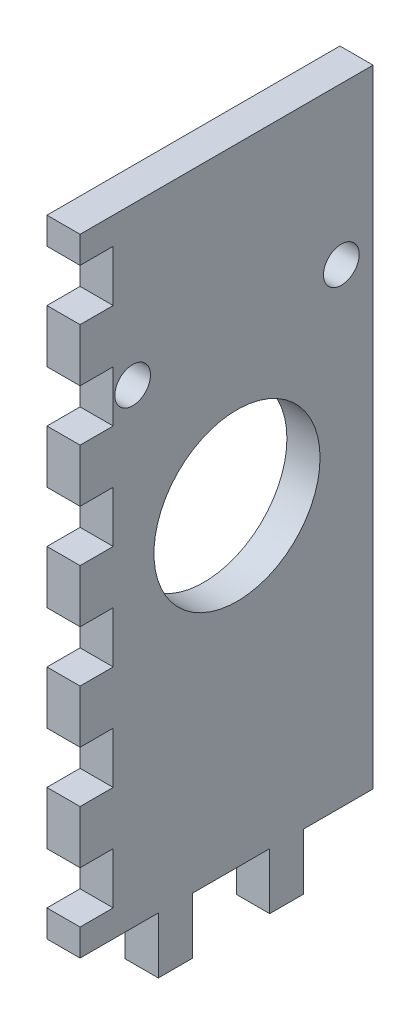
SolidWorks part; units mm, degrees
ref_plane "Front Plane" through (0, 0, 0) normal (0, 0, 1) x (1, 0, 0)
ref_plane "Top Plane" through (0, 0, 0) normal (0, 1, 0) x (1, 0, 0)
ref_plane "Right Plane" through (0, 0, 0) normal (1, 0, 0) x (0, 0, -1)
sketch "Sketch1" plane through (0, 0, 0) normal (0, 1, 0) x (1, 0, 0)
  line L0 (0, 0) -> (-50.5, 0) construction
  line L1 (0, 0) -> (0, 50.5) construction
  line L2 (-50.5, 22.5) -> (-22.5, 22.5)
  line L3 (-22.5, 22.5) -> (-22.5, 50.5)
  line L5 (-22.5, 22.5) -> (-50.5, 22.5)
  line L6 (-22.5, 22.5) -> (-22.5, 25.675)
  line L7 (-22.5, 25.675) -> (-50.5, 25.675)
  line L8 (-50.5, 22.5) -> (-50.5, 25.675)
  line L9 (-22.5, 22.5) -> (-25.675, 22.5)
  line L10 (-22.5, 22.5) -> (-22.5, 50.5)
  line L11 (-22.5, 50.5) -> (-25.675, 50.5)
  line L12 (-25.675, 22.5) -> (-25.675, 50.5)
  point P7 (-37.5, 22.5)
  point P8 (-22.5, 37.5)
  dimension "D1" = 50.5
  dimension "D2" = 50.5
  dimension "D3" = 22.5
  dimension "D4" = 22.5
  dimension "D5" = 37.5
  dimension "D6" = 37.5
  dimension "D7" = 28
  dimension "D8" = 28
  dimension "D9" = 3.175
  dimension "D10" = 3.175
extrude "Boss-Extrude1" add sketch "Sketch1" along normal blind 60 contours L2 L12 L7 L8 | L12 L5 L3 L7 | L12 L7 L3 L11
sketch "Sketch2" plane through (0, 0, -22.5) normal (0, 0, 1) x (1, 0, 0)
  line L0 (-50.5, 30) -> (-22.5, 30) construction
  line L1 (-50.5, 60) -> (-50.5, 0) construction
  line L2 (-22.5, 60) -> (-22.5, 0) construction
  line L3 (-37.5, 60) -> (-37.5, 0) construction
  line L4 (-50.5, 60) -> (-22.5, 60) construction
  line L5 (-50.5, 0) -> (-22.5, 0) construction
  line L7 (-50.5, 60) -> (-22.5758, 60)
  line L15 (-33.125, -5.4) -> (-33.125, 0)
  line L16 (-30, -5.4) -> (-33.125, -5.4)
  line L17 (-30, -5.4) -> (-30, 0)
  line L18 (-40.625, -5.4) -> (-40.625, 0)
  line L19 (-43.75, -5.4) -> (-40.625, -5.4)
  line L20 (-43.75, -5.4) -> (-43.75, 0)
  circle A0 centre (-37.5, 30) radius 8
  dimension "D2" = 16
  dimension "D1" = 15
  dimension "D3" = 5.4
  dimension "D4" = 7.5
  dimension "D6" = 3.125
  dimension "D5" = 7.5
sketch "Sketch3" plane through (-22.5, 0, 0) normal (1, 0, 0) x (0, 0, -1)
  line L0 (22.5, 30) -> (50.5, 30) construction
  line L1 (22.5, 60) -> (22.5, 0) construction
  line L2 (50.5, 60) -> (50.5, 0) construction
  line L3 (37.5, 60) -> (37.5, 0) construction
  line L4 (22.5, 60) -> (50.5, 60) construction
  line L5 (22.5, 0) -> (50.5, 0) construction
  circle A0 centre (37.5, 30) radius 8
  dimension "D1" = 16
  dimension "D2" = 15
extrude "Boss-Extrude4" add sketch "Sketch2" against normal blind 3.175
sketch "Sketch4" plane through (0, 0, -22.5) normal (0, 0, 1) x (1, 0, 0)
  line L0 (-50.5, 30) -> (-22.5, 30) construction
  line L1 (-50.5, 60) -> (-50.5, 0) construction
  line L2 (-22.5, 22) -> (-22.5, 38) construction
  line L3 (-37.5, 60) -> (-37.5, 0) construction
  line L4 (-50.5, 60) -> (-22.5, 60) construction
  line L5 (-50.5, 0) -> (-43.75, 0) construction
  line L6 (-22.5, 60) -> (-22.5, 0) construction
  circle A0 centre (-37.5, 30) radius 8
  dimension "D1" = 16
  dimension "D2" = 15
extrude "Cut-Extrude1" cut sketch "Sketch4" against normal blind 3.175
extrude "Cut-Extrude2" cut sketch "Sketch3" against normal blind 3.175
sketch "Sketch5" plane through (-22.5, 0, 0) normal (1, 0, 0) x (0, 0, -1)
  line L0 (22.5, 0) -> (50.5, 0) construction
  line L1 (22.5, 60) -> (50.5, 60)
  line L10 (22.5, 30) -> (50.5, 30) construction
  line L11 (22.5, 60) -> (22.5, 0) construction
  line L12 (50.5, 60) -> (50.5, 0) construction
  line L13 (43.85, -5.4) -> (43.85, 0)
  line L14 (40.675, -5.4) -> (43.85, -5.4)
  line L15 (40.675, -5.4) -> (40.675, 0)
  line L16 (33.175, -5.4) -> (33.175, 0)
  line L17 (30, -5.4) -> (33.175, -5.4)
  line L18 (30, -5.4) -> (30, 0)
  line L19 (30, 0) -> (33.175, 0)
  line L28 (40.675, 0) -> (43.85, 0)
  point P7 (37.5, 30)
  point P8 (-4.2304, -0.8722)
  point P10 (8.5502, 17.2274)
  dimension "D1" = 7.5
  dimension "D2" = 5.4
  dimension "D3" = 3.175
  dimension "D4" = 7.5
extrude "Boss-Extrude5" add sketch "Sketch5" against normal blind 3.175
sketch "Sketch6" plane through (0, 0, -22.5) normal (0, 0, 1) x (1, 0, 0)
  line L0 (-50.5, 45) -> (-22.5, 45) construction
  line L1 (-50.5, 60) -> (-50.5, 0) construction
  line L2 (-22.5, 60) -> (-22.5, 0) construction
  line L3 (-37.5, 60) -> (-37.5, 0) construction
  line L4 (-50.5, 60) -> (-22.5, 60) construction
  line L5 (-40.625, 0) -> (-33.125, 0) construction
  circle A0 centre (-37.5, 30) radius 8 construction
  circle A1 centre (-37.5, 30) radius 8 construction
  circle A2 centre (-47.5, 45) radius 1.75
  circle A3 centre (-27.5, 45) radius 1.75
  dimension "D1" = 15
  dimension "D3" = 3.5
  dimension "D2" = 10
extrude "Cut-Extrude3" cut sketch "Sketch6" against normal blind 10 contours A2 | A3
sketch "Sketch7" plane through (-22.5, 0, 0) normal (1, 0, 0) x (0, 0, -1)
  line L0 (37.5, 60) -> (37.5, 0) construction
  line L1 (22.5, 60) -> (50.5, 60) construction
  line L2 (33.175, 0) -> (40.675, 0) construction
  line L4 (22.5, 60) -> (22.5, 0) construction
  line L5 (22.5, 45) -> (50.5, 45) construction
  line L6 (50.5, 60) -> (50.5, 0) construction
  circle A0 centre (37.5, 30) radius 8 construction
  circle A1 centre (37.5, 30) radius 8 construction
  circle A2 centre (47.5, 45) radius 1.75
  circle A3 centre (27.5, 45) radius 1.75
  dimension "D1" = 15
  dimension "D3" = 3.5
  dimension "D2" = 10
extrude "Cut-Extrude4" cut sketch "Sketch7" against normal blind 10
sketch "Sketch9" plane through (-50.5, 0, 0) normal (-1, 0, 0) x (0, 0, 1)
  line L1 (-25.675, 60) -> (-22.5, 60)
  line L2 (-25.675, 60) -> (-25.675, -5.4)
  line L3 (-25.675, -5.4) -> (-22.5, -5.4)
  line L4 (-22.5, 60) -> (-22.5, -5.4)
extrude "Cut-Extrude5" cut sketch "Sketch9" along direction (-1, 0, 0) on the side against the normal up to surface (24.825 mm away)
sketch "Sketch10" plane through (-25.675, 0, 0) normal (-1, 0, 0) x (0, 0, 1)
  line L0 (-22.5, 60) -> (-22.5, 0) construction
  line L1 (-22.5, 57.5) -> (-25.675, 57.5)
  line L2 (-22.5, 57.5) -> (-22.5, 52.5)
  line L3 (-22.5, 52.5) -> (-25.675, 52.5)
  line L4 (-25.675, 57.5) -> (-25.675, 52.5)
  line L5 (-22.5, 47.5) -> (-25.675, 47.5)
  line L6 (-25.675, 47.5) -> (-25.675, 42.5)
  line L7 (-22.5, 42.5) -> (-25.675, 42.5)
  line L8 (-22.5, 47.5) -> (-22.5, 42.5)
  line L9 (-22.5, 37.5) -> (-25.675, 37.5)
  line L10 (-25.675, 37.5) -> (-25.675, 32.5)
  line L11 (-22.5, 32.5) -> (-25.675, 32.5)
  line L12 (-22.5, 37.5) -> (-22.5, 32.5)
  line L13 (-22.5, 27.5) -> (-25.675, 27.5)
  line L14 (-25.675, 27.5) -> (-25.675, 22.5)
  line L15 (-22.5, 22.5) -> (-25.675, 22.5)
  line L16 (-22.5, 27.5) -> (-22.5, 22.5)
  line L17 (-22.5, 17.5) -> (-25.675, 17.5)
  line L18 (-25.675, 17.5) -> (-25.675, 12.5)
  line L19 (-22.5, 12.5) -> (-25.675, 12.5)
  line L20 (-22.5, 17.5) -> (-22.5, 12.5)
  line L21 (-22.5, 7.5) -> (-25.675, 7.5)
  line L22 (-25.675, 7.5) -> (-25.675, 2.5)
  line L23 (-22.5, 2.5) -> (-25.675, 2.5)
  line L24 (-22.5, 7.5) -> (-22.5, 2.5)
  line L25 (-22.5, 60) -> (-50.5, 60) construction
  dimension "D1" = 3.175
  dimension "D2" = 5
  dimension "D4" = 2.5
  dimension "D5" = 5
  dimension "D3" = 6
extrude "Cut-Extrude6" cut sketch "Sketch10" against normal blind 10
sketch "Sketch11" plane through (-22.5, 0, 0) normal (1, 0, 0) x (0, 0, -1)
  line L73 (25.6344, 57.4594) -> (25.6344, 52.5406)
  line L74 (25.6344, 52.5406) -> (22.4594, 52.5406)
  line L75 (22.4594, 52.5406) -> (22.4594, 47.4594)
  line L76 (22.4594, 47.4594) -> (25.6344, 47.4594)
  line L77 (25.6344, 47.4594) -> (25.6344, 42.5406)
  line L78 (25.6344, 42.5406) -> (22.4594, 42.5406)
  line L79 (22.4594, 42.5406) -> (22.4594, 37.4594)
  line L80 (22.4594, 37.4594) -> (25.6344, 37.4594)
  line L81 (25.6344, 37.4594) -> (25.6344, 32.5406)
  line L82 (25.6344, 32.5406) -> (22.4594, 32.5406)
  line L83 (22.4594, 32.5406) -> (22.4594, 27.4594)
  line L84 (22.4594, 27.4594) -> (25.6344, 27.4594)
  line L85 (25.6344, 27.4594) -> (25.6344, 22.5406)
  line L86 (25.6344, 22.5406) -> (22.4594, 22.5406)
  line L87 (22.4594, 22.5406) -> (22.4594, 17.4594)
  line L88 (22.4594, 17.4594) -> (25.6344, 17.4594)
  line L89 (25.6344, 17.4594) -> (25.6344, 12.5406)
  line L90 (25.6344, 12.5406) -> (22.4594, 12.5406)
  line L91 (22.4594, 12.5406) -> (22.4594, 7.4594)
  line L92 (22.4594, 7.4594) -> (25.6344, 7.4594)
  line L93 (25.6344, 7.4594) -> (25.6344, 2.5406)
  line L94 (25.6344, 2.5406) -> (22.4594, 2.5406)
  line L95 (22.4594, 2.5406) -> (22.4594, -0.0406)
  line L96 (22.4594, -0.0406) -> (29.9594, -0.0406)
  line L97 (29.9594, -0.0406) -> (29.9594, -5.4406)
  line L98 (29.9594, -5.4406) -> (33.2156, -5.4406)
  line L99 (33.2156, -5.4406) -> (33.2156, -0.0406)
  line L100 (33.2156, -0.0406) -> (40.6344, -0.0406)
  line L101 (40.6344, -0.0406) -> (40.6344, -5.4406)
  line L102 (40.6344, -5.4406) -> (43.8906, -5.4406)
  line L103 (43.8906, -5.4406) -> (43.8906, -0.0406)
  line L104 (43.8906, -0.0406) -> (50.5406, -0.0406)
  line L105 (50.5406, -0.0406) -> (50.5406, 60.0406)
  line L106 (50.5406, 60.0406) -> (22.4594, 60.0406)
  line L107 (22.4594, 60.0406) -> (22.4594, 57.4594)
  line L108 (22.4594, 57.4594) -> (25.6344, 57.4594)
  line L109 (25.6344, 57.4594) -> (25.6344, 52.5406)
  line L110 (25.6344, 52.5406) -> (22.4594, 52.5406)
  line L111 (22.4594, 52.5406) -> (22.4594, 47.4594)
  line L112 (22.4594, 47.4594) -> (25.6344, 47.4594)
  line L113 (25.6344, 47.4594) -> (25.6344, 42.5406)
  line L114 (25.6344, 42.5406) -> (22.4594, 42.5406)
  line L115 (22.4594, 42.5406) -> (22.4594, 37.4594)
  line L116 (22.4594, 37.4594) -> (25.6344, 37.4594)
  line L117 (25.6344, 37.4594) -> (25.6344, 32.5406)
  line L118 (25.6344, 32.5406) -> (22.4594, 32.5406)
  line L119 (22.4594, 32.5406) -> (22.4594, 27.4594)
  line L120 (22.4594, 27.4594) -> (25.6344, 27.4594)
  line L121 (25.6344, 27.4594) -> (25.6344, 22.5406)
  line L122 (25.6344, 22.5406) -> (22.4594, 22.5406)
  line L123 (22.4594, 22.5406) -> (22.4594, 17.4594)
  line L124 (22.4594, 17.4594) -> (25.6344, 17.4594)
  line L125 (25.6344, 17.4594) -> (25.6344, 12.5406)
  line L126 (25.6344, 12.5406) -> (22.4594, 12.5406)
  line L127 (22.4594, 12.5406) -> (22.4594, 7.4594)
  line L128 (22.4594, 7.4594) -> (25.6344, 7.4594)
  line L129 (25.6344, 7.4594) -> (25.6344, 2.5406)
  line L130 (25.6344, 2.5406) -> (22.4594, 2.5406)
  line L131 (22.4594, 2.5406) -> (22.4594, -0.0406)
  line L132 (22.4594, -0.0406) -> (29.9594, -0.0406)
  line L133 (29.9594, -0.0406) -> (29.9594, -5.4406)
  line L134 (29.9594, -5.4406) -> (33.2156, -5.4406)
  line L135 (33.2156, -5.4406) -> (33.2156, -0.0406)
  line L136 (33.2156, -0.0406) -> (40.6344, -0.0406)
  line L137 (40.6344, -0.0406) -> (40.6344, -5.4406)
  line L138 (40.6344, -5.4406) -> (43.8906, -5.4406)
  line L139 (43.8906, -5.4406) -> (43.8906, -0.0406)
  line L140 (43.8906, -0.0406) -> (50.5406, -0.0406)
  line L141 (50.5406, -0.0406) -> (50.5406, 60.0406)
  line L142 (50.5406, 60.0406) -> (22.4594, 60.0406)
  line L143 (22.4594, 60.0406) -> (22.4594, 57.4594)
  line L144 (22.4594, 57.4594) -> (25.6344, 57.4594)
  circle A2 centre (37.5, 30) radius 7.9594
  circle A4 centre (37.5, 30) radius 7.9594
  circle A6 centre (27.5, 45) radius 1.7094
  circle A7 centre (27.5, 45) radius 1.7094
  circle A9 centre (47.5, 45) radius 1.7094
  circle A10 centre (47.5, 45) radius 1.7094
  dimension "D1" = 0.0406
  dimension "D2" = 0.0406
  dimension "D3" = 0.0406
  dimension "D4" = 0.0406
extrude "Boss-Extrude6" add sketch "Sketch11" against normal up to surface (3.175 mm away) up to face at (-25.675, 22.7333, -28.3194)
equation "\"wall width\"=5.05"
equation "\"D1@Sketch1\"=\"wall width\""
equation "\"D2@Sketch1\"=\"wall width\""
equation "\"belt traveling width\"=2.25"
equation "\"D3@Sketch1\"=\"belt traveling width\""
equation "\"D4@Sketch1\"=\"belt traveling width\""
equation "\"bearing center\"=3.75"
equation "\"D5@Sketch1\"=\"bearing center\""
equation "\"D6@Sketch1\"=\"bearing center\""
equation "\"bearing holder wall width\"=2.8"
equation "\"D7@Sketch1\"=\"bearing holder wall width\""
equation "\"D8@Sketch1\"=\"bearing holder wall width\""
equation "\"wall thickness\"=0.3175"
equation "\"D9@Sketch1\"=\"wall thickness\""
equation "\"D10@Sketch1\"=\"wall thickness\""
equation "\"off wall bearing distance\"=1.5"
equation "\"D1@Sketch2\"=\"off wall bearing distance\""
equation "\"bearing diameter\"=1.6"
equation "\"D2@Sketch2\"=\"bearing diameter\""
equation "\"D1@Sketch3\"=\"bearing diameter\""
equation "\"D2@Sketch3\"=\"off wall bearing distance\""
equation "\"tooth width\"=0.75"
equation "\"D1@Sketch4\"=\"bearing diameter\""
equation "\"D2@Sketch4\"=\"off wall bearing distance\""
equation "\"D1@Sketch10\"=\"wall thickness\""
